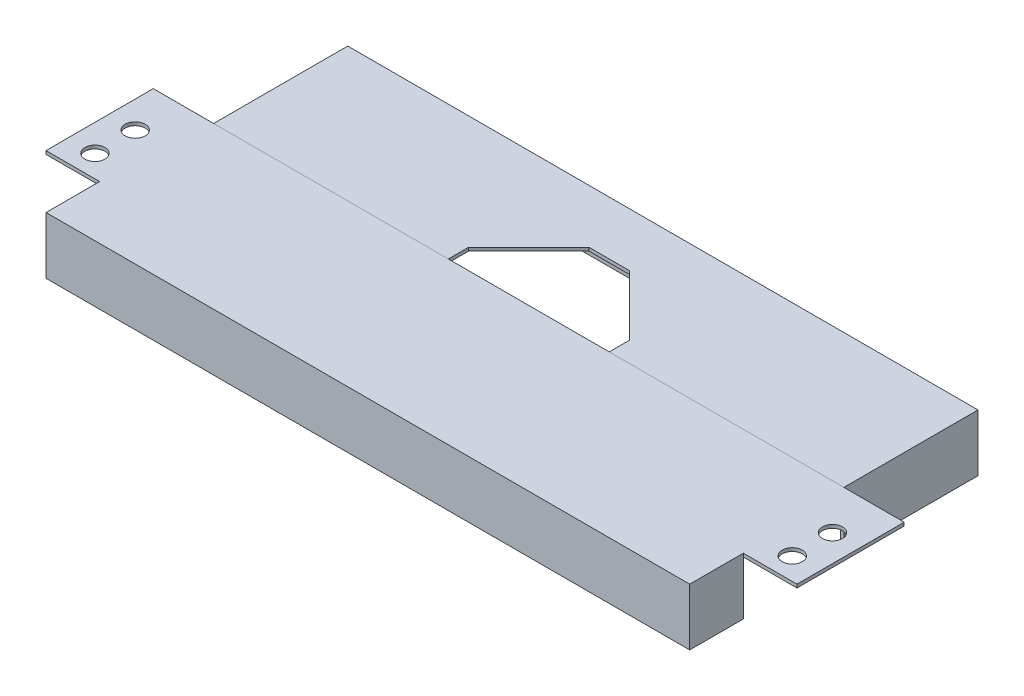
SolidWorks part; units mm, degrees
ref_plane "Front Plane" through (0, 0, 0) normal (0, 0, 1) x (1, 0, 0)
ref_plane "Top Plane" through (0, 0, 0) normal (0, 1, 0) x (1, 0, 0)
ref_plane "Right Plane" through (0, 0, 0) normal (1, 0, 0) x (0, 0, -1)
sketch "Sketch1" plane through (0, 0, 0) normal (0, 1, 0) x (1, 0, 0)
  line L0 (222.25, 0) -> (222.25, 76.2)
  line L1 (0, 0) -> (222.25, 0)
  line L2 (0, 0) -> (0, 127)
  line L3 (0, 127) -> (596.9, 127)
  line L4 (596.9, 0) -> (596.9, 127)
  line L5 (222.25, 76.2) -> (374.65, 76.2)
  line L6 (374.65, 76.2) -> (374.65, 0)
  line L7 (298.45, 127) -> (298.45, 76.2) construction
  line L8 (374.65, 0) -> (596.9, 0)
  dimension "D3" = 76.2
  dimension "D4" = 152.4
  dimension "D1" = 127
  dimension "D2" = 596.9
extrude "Boss-Extrude1" add sketch "Sketch1" along normal blind 3.175
chamfer "Chamfer1" distance 57.15 angle 45 2 edges at (374.65, 1.5875, -76.2) (222.25, 1.5875, -76.2)
sketch "Sketch2" plane through (0, 0, 0) normal (0, -1, 0) x (-1, 0, 0)
  line L0 (0, 0) -> (-3.175, 0)
  line L1 (0, 0) -> (-222.25, 0) construction
  line L2 (-3.175, 0) -> (-3.175, 127)
  line L3 (-596.9, 127) -> (0, 127) construction
  line L4 (-3.175, 127) -> (0, 127)
  line L5 (0, 127) -> (0, 0)
  dimension "D1" = 3.175
extrude "Boss-Extrude2" add sketch "Sketch2" along normal blind 50.8 separate body
sketch "Sketch3" plane through (0, 0, 0) normal (0, -1, 0) x (-1, 0, 0)
  line L0 (-596.9, 0) -> (-596.9, 127)
  line L1 (-596.9, 127) -> (-593.725, 127)
  line L2 (-596.9, 127) -> (0, 127) construction
  line L3 (-593.725, 127) -> (-593.725, 0)
  line L4 (-374.65, 0) -> (-596.9, 0) construction
  line L5 (-593.725, 0) -> (-596.9, 0)
  dimension "D1" = 3.175
extrude "Boss-Extrude3" add sketch "Sketch3" along normal blind 50.8
sketch "Sketch4" plane through (0, 0, 0) normal (0, 0, 1) x (1, 0, 0)
  line L0 (0, 3.175) -> (-57.15, 3.175)
  line L1 (-57.15, 3.175) -> (-57.15, 0)
  line L2 (-57.15, 0) -> (0, 0)
  line L3 (0, 0) -> (596.9, 0)
  line L4 (596.9, 3.175) -> (596.9, -50.8) construction
  line L5 (596.9, 0) -> (654.05, 0)
  line L6 (654.05, 0) -> (654.05, 3.175)
  line L7 (654.05, 3.175) -> (596.9, 3.175)
  line L8 (596.9, 3.175) -> (0, 3.175)
  dimension "D1" = 57.15
  dimension "D2" = 57.15
extrude "Boss-Extrude4" add sketch "Sketch4" along normal blind 101.6 separate body
sketch "Sketch5" plane through (0, 0, 101.6) normal (0, 0, 1) x (1, 0, 0)
  line L0 (-6.35, 3.175) -> (-6.35, 0)
  line L1 (654.05, 3.175) -> (-57.15, 3.175) construction
  line L2 (-57.15, 0) -> (654.05, 0) construction
  line L3 (-6.35, 0) -> (603.25, 0)
  line L4 (603.25, 0) -> (603.25, 3.175)
  line L5 (603.25, 3.175) -> (-6.35, 3.175)
  line L6 (-57.15, 3.175) -> (-57.15, 0) construction
  line L7 (654.05, 0) -> (654.05, 3.175) construction
  point P6 (-57.15, 1.5875)
  dimension "D1" = 50.8
  dimension "D2" = 50.8
extrude "Boss-Extrude5" add sketch "Sketch5" along normal blind 50.8 separate body
sketch "Sketch6" plane through (0, 0, 0) normal (0, -1, 0) x (-1, 0, 0)
  line L0 (-603.25, -101.6) -> (-600.075, -101.6)
  line L1 (57.15, -101.6) -> (-654.05, -101.6) construction
  line L2 (-600.075, -101.6) -> (-600.075, -149.225)
  line L3 (-600.075, -149.225) -> (3.175, -149.225)
  line L4 (3.175, -149.225) -> (3.175, -101.6)
  line L7 (6.35, -101.6) -> (6.35, -152.4)
  line L8 (6.35, -152.4) -> (-603.25, -152.4)
  line L9 (-603.25, -152.4) -> (-603.25, -101.6) construction
  line L10 (3.175, -101.6) -> (6.35, -101.6)
  line L14 (6.35, -101.6) -> (-603.25, -101.6)
  line L15 (-603.25, -101.6) -> (-603.25, -152.4)
  line L16 (-603.25, -152.4) -> (6.35, -152.4)
  line L17 (6.35, -152.4) -> (6.35, -101.6)
  line L19 (-603.25, -101.6) -> (-603.25, -152.4)
  dimension "D1" = 3.175
  dimension "D2" = 3.175
  dimension "D3" = 3.175
  dimension "D4" = 0
extrude "Boss-Extrude6" add sketch "Sketch6" along normal blind 50.8
sketch "Sketch7" plane through (0, 0, 0) normal (0, -1, 0) x (1, 0, 0)
  line L0 (593.725, -127) -> (3.175, -127)
  line L1 (3.175, -127) -> (3.175, -123.825)
  line L2 (3.175, -127) -> (3.175, 0) construction
  line L3 (3.175, -123.825) -> (593.725, -123.825)
  line L4 (593.725, 0) -> (593.725, -127) construction
  line L5 (593.725, -123.825) -> (593.725, -127)
  dimension "D1" = 3.175
extrude "Boss-Extrude7" add sketch "Sketch7" along normal blind 50.8 separate body
sketch "Sketch8" plane through (0, 3.175, 0) normal (0, 1, 0) x (1, 0, 0)
  line L0 (298.45, -152.4) -> (298.45, 0) construction
  line L1 (603.25, -152.4) -> (-6.35, -152.4) construction
  line L2 (654.05, 0) -> (-57.15, 0) construction
  line L4 (-57.15, -101.6) -> (-57.15, 0) construction
  line L6 (-6.35, -101.6) -> (-57.15, -101.6) construction
  circle A0 centre (-31.75, -80.645) radius 9.525
  circle A1 centre (-31.75, -42.545) radius 9.525
  circle A2 centre (628.65, -42.545) radius 9.525
  circle A3 centre (628.65, -80.645) radius 9.525
  dimension "D1" = 19.05
  dimension "D2" = 25.4
  dimension "D3" = 20.955
  dimension "D4" = 2
extrude "Cut-Extrude1" cut sketch "Sketch8" against normal through all
